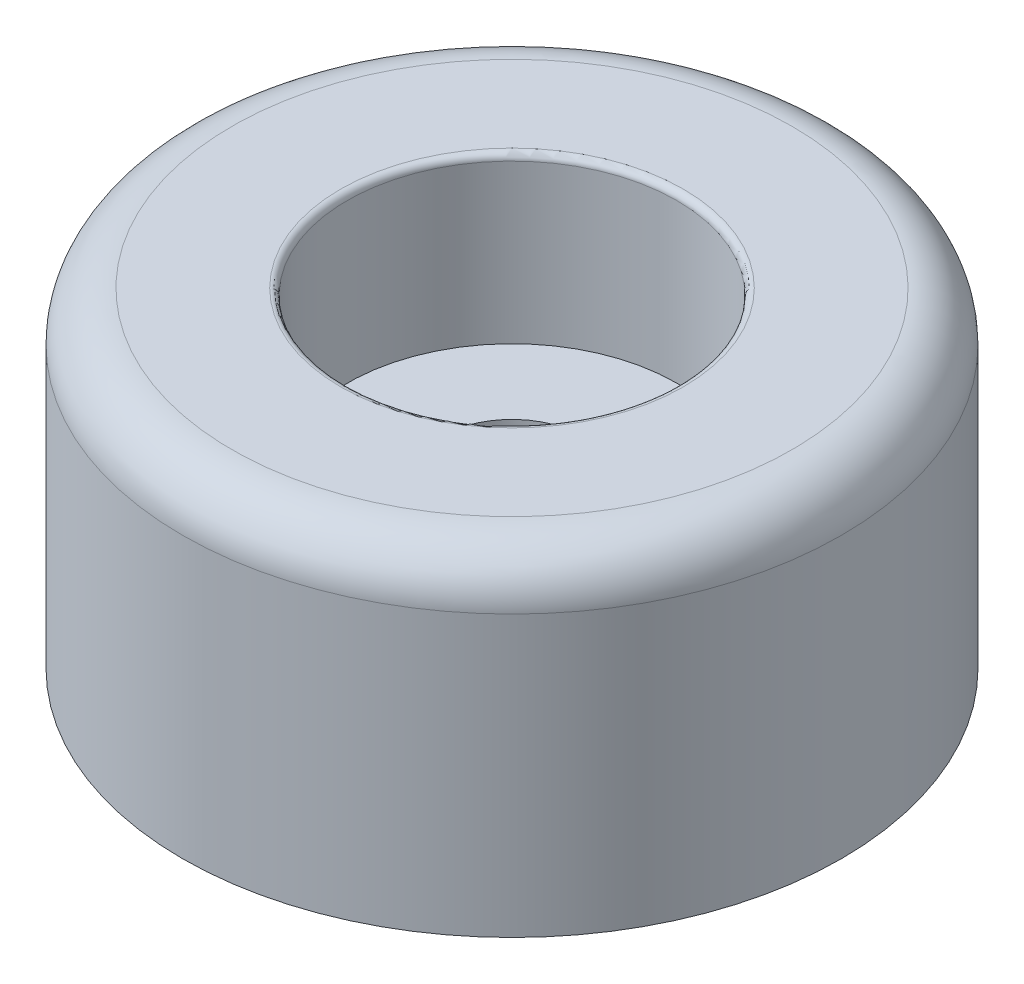
SolidWorks part; units mm, degrees
material "Rubber"
ref_plane "Front" through (0, 0, 0) normal (0, 0, 1) x (1, 0, 0)
ref_plane "Top" through (0, 0, 0) normal (0, 1, 0) x (1, 0, 0)
ref_plane "Right" through (0, 0, 0) normal (1, 0, 0) x (0, 0, -1)
sketch "Sketch1" plane through (0, 0, 0) normal (0, 0, 1) x (1, 0, 0)
  line L0 (12.7, 0) -> (-12.7, 0) construction
  line L1 (0, 0) -> (0, 12.7) construction
  line L2 (6.35, 6.35) -> (-6.35, 6.35) construction
  line L3 (2.7781, 0) -> (-2.7781, 0) construction
  point P7 (0, 6.35)
  dimension "OD" = 25.4
  dimension "Height" = 12.7
  dimension "Counterbore Dia" = 12.7
  dimension "Mounting Surface Ht" = 6.35
  dimension "Mounting Hole Dia" = 5.5562
sketch "Sketch2" plane through (0, 0, 0) normal (0, 0, 1) x (1, 0, 0)
  line L0 (-12.7, 0) -> (-12.7, 10.795)
  line L1 (-10.795, 12.7) -> (-6.35, 12.7)
  line L2 (-6.35, 12.7) -> (-6.35, 6.35)
  line L3 (-6.35, 6.35) -> (-2.7781, 6.35)
  line L4 (6.35, 6.35) -> (-6.35, 6.35) construction
  line L5 (-2.7781, 6.35) -> (-2.7781, 0)
  line L6 (-2.7781, 0) -> (-12.7, 0)
  arc A0 (-10.795, 12.7) -> (-12.7, 10.795) centre (-10.795, 10.795) ccw
  dimension "D1" = 1.905
revolve "Revolve1" add sketch "Sketch2" angle 360 about L1
fillet "Fillet1" radius 0.254 1 edges at (0, 12.7, -6.35)
sketch "Sketch3" plane through (0, 0, 0) normal (0, 0, 1) x (1, 0, 0)
  line L0 (-2.7781, 6.35) -> (-2.7781, 0) construction
  line L1 (2.7781, 0) -> (2.7781, 6.35) construction
  line L2 (-6.35, 12.446) -> (-6.35, 6.35) construction
  line L3 (6.35, 6.35) -> (6.35, 12.446) construction
  line L4 (-2.7781, 6.35) -> (-2.7781, 0)
  line L5 (2.7781, 0) -> (2.7781, 6.35)
  line L6 (-6.35, 12.446) -> (-6.35, 6.35)
  line L7 (6.35, 6.35) -> (6.35, 12.446)
  line L8 (-6.35, 6.35) -> (-2.7781, 6.35)
  line L9 (2.7781, 6.35) -> (6.35, 6.35)
  arc A0 (-6.35, 12.446) -> (-6.604, 12.7) centre (-6.604, 12.446) ccw construction
  arc A1 (6.604, 12.7) -> (6.35, 12.446) centre (6.604, 12.446) ccw construction
  arc A2 (-6.35, 12.446) -> (-6.604, 12.7) centre (-6.604, 12.446) ccw
  arc A3 (6.604, 12.7) -> (6.35, 12.446) centre (6.604, 12.446) ccw
equation "\"D1@Sketch2\"=\"Height@Sketch1\"*.15"
equation "\"D1@Fillet1\"=\"OD@Sketch1\"*.01"
